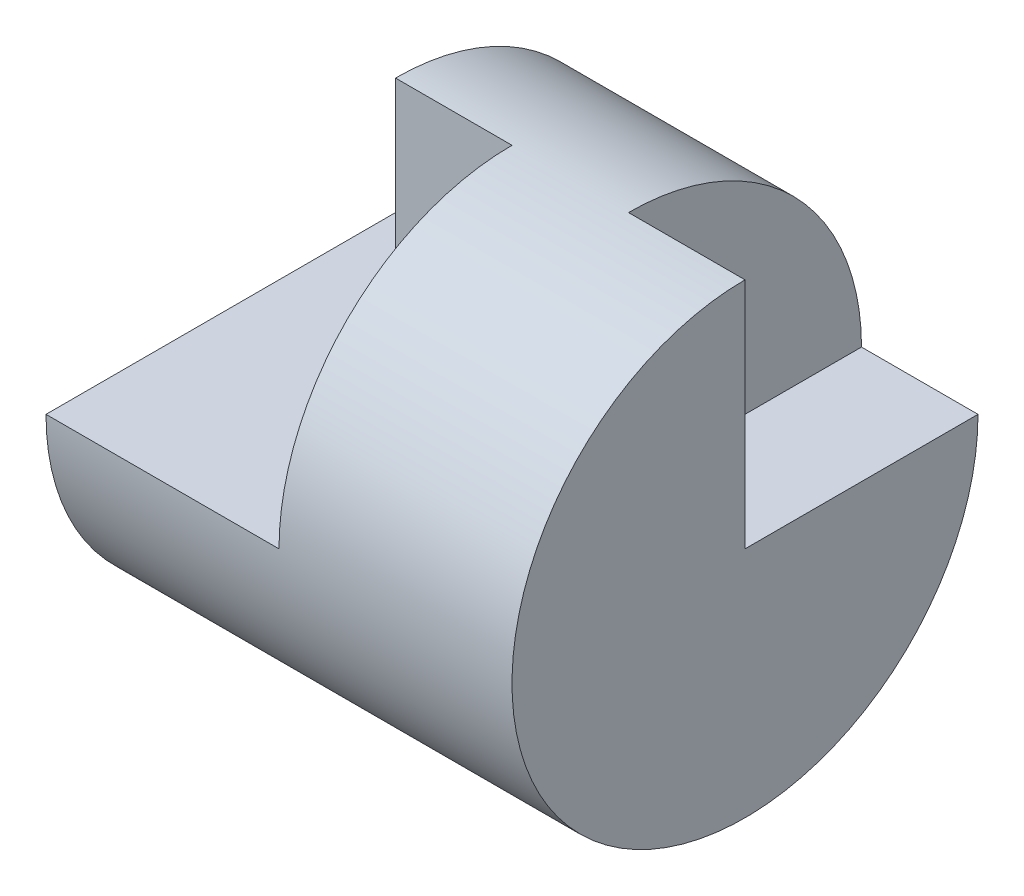
SolidWorks part; units mm, degrees
ref_plane "Front Plane" through (0, 0, 0) normal (0, 0, 1) x (1, 0, 0)
ref_plane "Top Plane" through (0, 0, 0) normal (0, 1, 0) x (1, 0, 0)
ref_plane "Right Plane" through (0, 0, 0) normal (1, 0, 0) x (0, 0, -1)
sketch "Sketch5" plane through (0, 0, 0) normal (0, 0, 1) x (1, 0, 0)
  line L0 (0, 0) -> (4, 0)
  dimension "D1" = 4
revolve "Revolve-Thin2" add sketch "Sketch5" angle 360 about L0 wall 2
sketch "Sketch6" plane through (0, 0, 0) normal (0, 0, 1) x (1, 0, 0)
  line L1 (0, 2) -> (1, 2)
  line L2 (0, 2) -> (0, 0)
  line L3 (0, 0) -> (1, 0)
  line L4 (1, 2) -> (1, 0)
  line L5 (4, 2) -> (3, 2)
  line L6 (4, 2) -> (4, 0)
  line L7 (4, 0) -> (3, 0)
  line L8 (3, 2) -> (3, 0)
  dimension "D1" = 1
  dimension "D2" = 1
  dimension "D3" = 2
  dimension "D4" = 2
extrude "Cut-Extrude5" cut sketch "Sketch6" against normal blind 11 contours L5 L8 L7 L6 | L4 L1 L2 L3
sketch "Sketch8" plane through (0, 0, 0) normal (0, 0, -1) x (-1, 0, 0)
  line L0 (0, 0) -> (-1, 0) construction
  line L1 (0, 2) -> (-0.5, 2)
  line L2 (0, 2) -> (0, 0)
  line L3 (0, 0) -> (-0.5, 0)
  line L4 (-0.5, 2) -> (-0.5, 0)
extrude "Cut-Extrude7" cut sketch "Sketch8" against normal blind 10
sketch "Sketch9" plane through (0, 0, 0) normal (0, 0, -1) x (-1, 0, 0)
  line L0 (-1, 2) -> (-3, 2) construction
  line L5 (-0.5, 0) -> (-2, 0)
  line L6 (-0.5, 0) -> (-0.5, 2)
  line L7 (-0.5, 2) -> (-2, 2)
  line L8 (-2, 0) -> (-2, 2)
  line L9 (-4, 2) -> (-4, 0) construction
  dimension "D1" = 2
extrude "Cut-Extrude8" cut sketch "Sketch9" against normal blind 10
